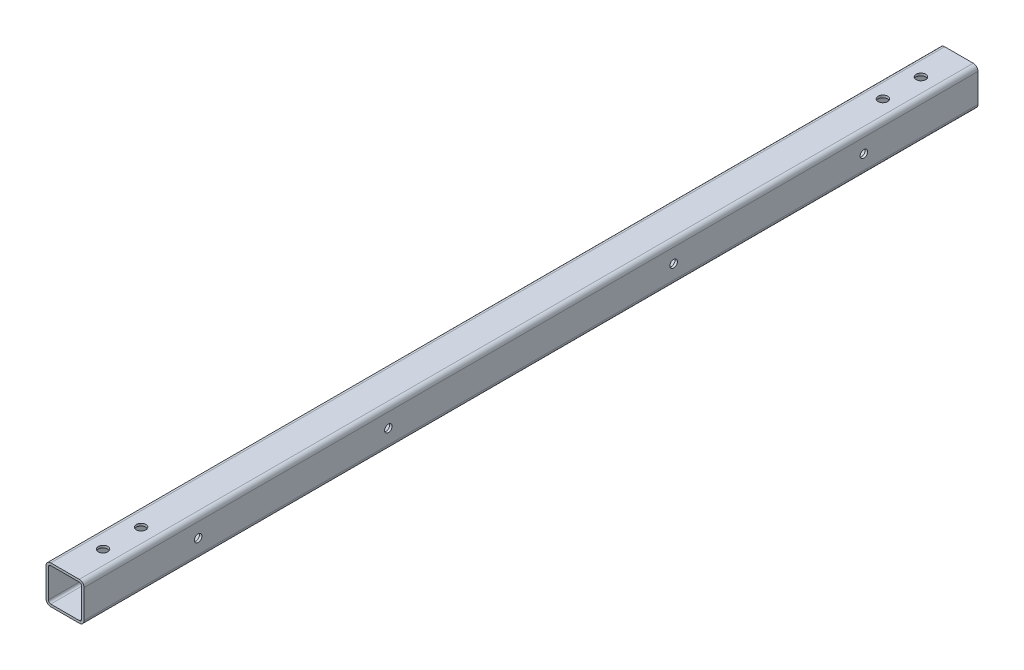
SolidWorks part; units mm, degrees
material "3003 Alloy"
ref_plane "Front" through (0, 0, 0) normal (0, 0, 1) x (1, 0, 0)
ref_plane "Top" through (0, 0, 0) normal (0, 1, 0) x (1, 0, 0)
ref_plane "Right" through (0, 0, 0) normal (1, 0, 0) x (0, 0, -1)
sketch "Sketch1" plane through (0, 0, 0) normal (0, 0, 1) x (1, 0, 0)
  line L0 (-12.7, 12.7) -> (12.7, 12.7)
  line L1 (-12.7, 12.7) -> (-12.7, -12.7)
  line L2 (12.7, -12.7) -> (-12.7, -12.7)
  line L3 (12.7, -12.7) -> (12.7, 12.7)
  line L4 (-12.7, -12.7) -> (12.7, 12.7) construction
  dimension "square" = 25.4
extrude "Base-Extrude" add sketch "Sketch1" along normal mid plane 596.9
fillet "Fillet1" radius 3.175 4 edges at (-12.7, 12.7, 0) (12.7, 12.7, 0) (12.7, -12.7, 0) (-12.7, -12.7, 0)
shell "Shell1" thickness 1.5875
sketch "Sketch3" plane through (-12.7, 0, 0) normal (-1, 0, 0) x (0, 0, 1)
  line L0 (-298.45, 0) -> (-158.75, 0) construction
  line L1 (-298.45, 9.525) -> (-298.45, -9.525) construction
  circle A0 centre (-209.55, 0) radius 3.175
  circle A2 centre (-158.75, 0) radius 3.175
  dimension "D2" = 6.35
  dimension "D1" = 139.7
  dimension "D3" = 88.9
extrude "tank" [suppressed] cut sketch "Sketch3" against normal up to next
sketch "Sketch4" plane through (0, -12.7, 0) normal (0, -1, 0) x (1, 0, 0)
  line L4 (0, 298.45) -> (0, -298.45) construction
  line L7 (9.525, 298.45) -> (-9.525, 298.45) construction
  line L8 (9.525, -298.45) -> (-9.525, -298.45) construction
  circle A4 centre (0, 273.05) radius 3.175
  circle A5 centre (0, 247.65) radius 3.175
  circle A6 centre (0, -247.65) radius 3.175
  circle A7 centre (0, -273.05) radius 3.175
  dimension "D5" = 6.35
  dimension "D1" = 25.4
  dimension "D2" = 50.8
  dimension "D3" = 25.4
  dimension "D4" = 50.8
extrude "Cut-Extrude1" cut sketch "Sketch4" against normal through all
sketch "Sketch5" plane through (0, -12.7, 0) normal (0, -1, 0) x (1, 0, 0)
  line L0 (0, -298.45) -> (0, 298.45) construction
  line L1 (9.525, -298.45) -> (-9.525, -298.45) construction
  line L2 (9.525, 298.45) -> (-9.525, 298.45) construction
  circle A2 centre (0, 273.05) radius 3.175
  circle A3 centre (0, 247.65) radius 3.175
  circle A6 centre (0, -273.05) radius 3.175
  circle A7 centre (0, -247.65) radius 3.175
  dimension "D3" = 6.35
  dimension "D1" = 25.4
  dimension "D2" = 50.8
  dimension "D4" = 50.8
  dimension "D5" = 25.4
extrude "Cut-Extrude2" [suppressed] cut sketch "Sketch5" against normal through all
sketch "Sketch6" plane through (11.1125, 0, 0) normal (-1, 0, 0) x (0, 0, 1)
  line L0 (-298.45, 9.525) -> (-298.45, -9.525) construction
  line L1 (298.45, 9.525) -> (298.45, -9.525) construction
  line L2 (298.45, -12.7) -> (-298.45, -12.7) construction
  circle A2 centre (-95.25, 0) radius 2.5
  circle A3 centre (-222.25, 0) radius 2.5
  circle A6 centre (222.25, 0) radius 2.5
  circle A7 centre (95.25, 0) radius 2.5
  dimension "D1" = 76.2
  dimension "D2" = 127
  dimension "D3" = 127
  dimension "D4" = 76.2
  dimension "D5" = 12.7
extrude "Cut-Extrude3" cut sketch "Sketch6" against normal up to next
